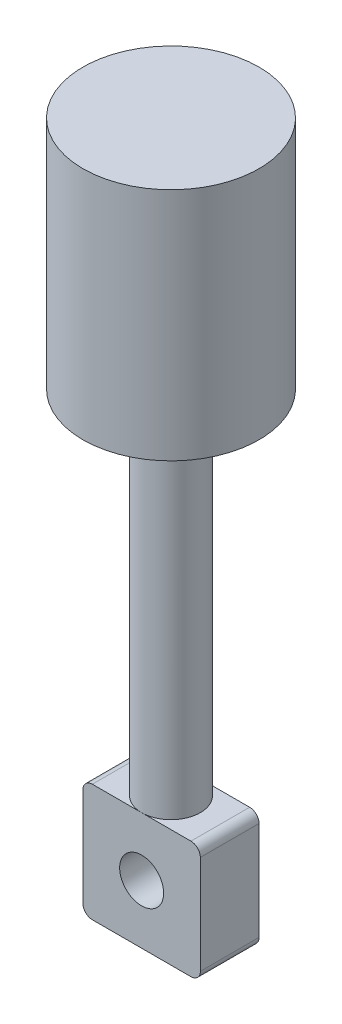
SolidWorks part; units mm, degrees
material "Cast Alloy Steel"
ref_plane "Front Plane" through (0, 0, 0) normal (0, 0, 1) x (1, 0, 0)
ref_plane "Top Plane" through (0, 0, 0) normal (0, 1, 0) x (1, 0, 0)
ref_plane "Right Plane" through (0, 0, 0) normal (1, 0, 0) x (0, 0, -1)
sketch "Sketch2" plane through (0, 0, 0) normal (0, 0, 1) x (1, 0, 0)
  line L1 (-2.667, 3.175) -> (-1.5875, 3.175)
  line L2 (-3.175, 2.667) -> (-3.175, -2.667)
  line L3 (-2.667, -3.175) -> (2.667, -3.175)
  line L4 (3.175, 2.667) -> (3.175, -2.667)
  line L5 (-1.5875, 3.175) -> (1.5875, 3.175)
  line L9 (1.5875, 3.175) -> (2.667, 3.175)
  circle A0 centre (0, 0) radius 1.1906
  arc A1 (-3.175, -2.667) -> (-2.667, -3.175) centre (-2.667, -2.667) ccw
  arc A2 (2.667, -3.175) -> (3.175, -2.667) centre (2.667, -2.667) ccw
  arc A3 (2.667, 3.175) -> (3.175, 2.667) centre (2.667, 2.667) cw
  arc A4 (-2.667, 3.175) -> (-3.175, 2.667) centre (-2.667, 2.667) ccw
  point P12 (0, -3.175)
  point P13 (-3.175, 0)
  point P16 (-3.175, -3.175)
  point P19 (3.175, -3.175)
  point P24 (-3.175, 3.175)
  dimension "D3" = 2.3813
  dimension "D6" = 0.508
  dimension "D1" = 6.35
  dimension "D2" = 6.35
extrude "Boss-Extrude2" add sketch "Sketch2" along normal mid plane 3.175
sketch "Sketch6" plane through (0, 3.175, 0) normal (0, 1, 0) x (1, 0, 0)
  circle A0 centre (0, 0) radius 1.5875
  dimension "D1" = 3.175
extrude "Boss-Extrude5" add sketch "Sketch6" along normal blind 19.05
sketch "Sketch7" plane through (0, 22.225, 0) normal (0, 1, 0) x (1, 0, 0)
  circle A0 centre (0, 0) radius 4.7625
  dimension "D1" = 9.525
extrude "Boss-Extrude6" add sketch "Sketch7" along normal blind 12.7
